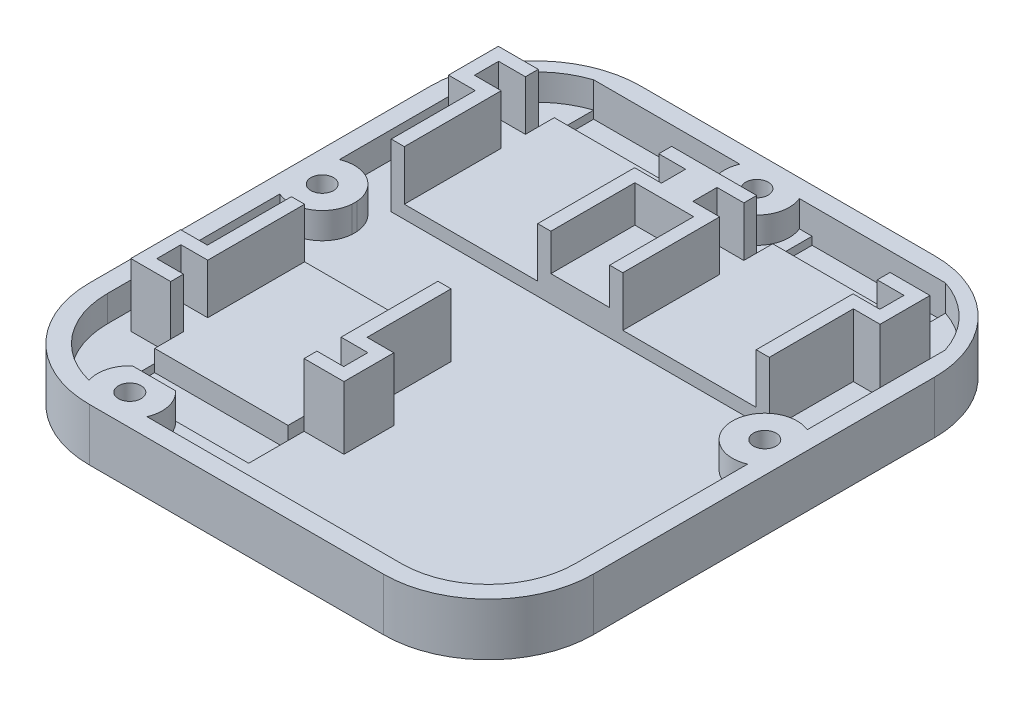
SolidWorks part; units mm, degrees
material "ABS"
ref_plane "Front Plane" through (0, 0, 0) normal (0, 0, 1) x (1, 0, 0)
ref_plane "Top Plane" through (0, 0, 0) normal (0, 1, 0) x (1, 0, 0)
ref_plane "Right Plane" through (0, 0, 0) normal (1, 0, 0) x (0, 0, -1)
sketch "Sketch1" plane through (0, 0, 0) normal (0, 1, 0) x (1, 0, 0)
  line L0 (-28, 52.5) -> (28, 52.5)
  line L1 (48, 32.5) -> (48, -32.5)
  line L2 (28, -52.5) -> (-28, -52.5)
  line L3 (-48, -32.5) -> (-48, 32.5)
  line L4 (0, 52.5) -> (0, -52.5) construction
  line L5 (-48, 0) -> (48, 0) construction
  arc A0 (-28, -52.5) -> (-48, -32.5) centre (-28, -32.5) cw
  arc A1 (48, -32.5) -> (28, -52.5) centre (28, -32.5) cw
  arc A2 (48, 32.5) -> (28, 52.5) centre (28, 32.5) ccw
  arc A3 (-28, 52.5) -> (-48, 32.5) centre (-28, 32.5) ccw
  point P8 (0, 0)
  point P14 (48, -52.5)
  point P17 (48, 52.5)
  point P20 (-48, 52.5)
  dimension "D1" = 96
  dimension "D3" = 20
  dimension "D2" = 105
extrude "base" add sketch "Sketch1" along normal blind 10
sketch "Sketch10" plane through (0, 10, 0) normal (0, 1, 0) x (1, 0, 0)
  line L0 (-41.1, -22) -> (-41.1, -31.5) construction
  line L1 (-41.1, -31.5) -> (-0.5, -31.5) construction
  line L2 (-41.1, -22) -> (-41.1, -31.5)
  line L3 (-41.1, -31.5) -> (-0.5, -31.5)
  line L4 (-28, -52.5) -> (28, -52.5)
  line L5 (-48, 32.5) -> (-48, -32.5)
  line L6 (28, 52.5) -> (-28, 52.5)
  line L7 (48, -32.5) -> (48, 32.5)
  line L8 (-28, -52.5) -> (28, -52.5)
  line L9 (-48, 32.5) -> (-48, -32.5)
  line L10 (28, 52.5) -> (-28, 52.5)
  line L11 (48, -32.5) -> (48, 32.5)
  line L12 (-3, -24.45) -> (-3, -29.05) construction
  line L13 (-3, -29.05) -> (-38.6, -29.05) construction
  line L14 (-38.6, -29.05) -> (-38.6, -24.45) construction
  line L15 (-38.6, -24.45) -> (-3, -24.45) construction
  line L16 (-41.1, -22) -> (-41.1, -31.5)
  line L17 (-41.1, -31.5) -> (-0.5, -31.5)
  line L18 (-0.5, -31.5) -> (-0.5, -22)
  line L19 (-0.5, -22) -> (-8.6, -22)
  line L20 (-8.6, -22) -> (-8.6, -6)
  line L21 (-8.6, -6) -> (-33, -6)
  line L22 (-33, -6) -> (-33, -22)
  line L23 (-33, -22) -> (-41.1, -22)
  line L24 (-41.1, -22) -> (-41.1, -31.5)
  line L25 (-41.1, -31.5) -> (-0.5, -31.5)
  line L26 (-0.5, -31.5) -> (-0.5, -22)
  line L27 (-0.5, -22) -> (-8.6, -22)
  line L28 (-8.6, -22) -> (-8.6, -6)
  line L29 (-8.6, -6) -> (-33, -6)
  line L30 (-33, -6) -> (-33, -22)
  line L31 (-33, -22) -> (-41.1, -22)
  line L32 (-12.6, -10) -> (-12.6, -22) construction
  line L33 (-12.6, -22) -> (-29, -22) construction
  line L34 (-29, -22) -> (-29, -10) construction
  line L35 (-29, -10) -> (-12.6, -10) construction
  line L36 (41.1, 29) -> (41.1, 38.5)
  line L37 (41.1, 38.5) -> (-41.1, 38.5)
  line L38 (-41.1, 38.5) -> (-41.1, 29)
  line L39 (-41.1, 29) -> (-33, 29)
  line L40 (-33, 29) -> (-33, 13)
  line L41 (-33, 13) -> (-8.6, 13)
  line L42 (-8.6, 13) -> (-8.6, 29)
  line L43 (-8.6, 29) -> (8.6, 29)
  line L44 (8.6, 29) -> (8.6, 13)
  line L45 (8.6, 13) -> (33, 13)
  line L46 (33, 13) -> (33, 29)
  line L47 (33, 29) -> (41.1, 29)
  line L48 (41.1, 29) -> (41.1, 38.5)
  line L49 (41.1, 38.5) -> (-41.1, 38.5)
  line L50 (-41.1, 38.5) -> (-41.1, 29)
  line L51 (-41.1, 29) -> (-33, 29)
  line L52 (-33, 29) -> (-33, 13)
  line L53 (-33, 13) -> (-8.6, 13)
  line L54 (-8.6, 13) -> (-8.6, 29)
  line L55 (-8.6, 29) -> (8.6, 29)
  line L56 (8.6, 29) -> (8.6, 13)
  line L57 (8.6, 13) -> (33, 13)
  line L58 (33, 13) -> (33, 29)
  line L59 (33, 29) -> (41.1, 29)
  line L60 (-29, 17) -> (-29, 29) construction
  line L61 (-29, 29) -> (-12.6, 29) construction
  line L62 (-12.6, 29) -> (-12.6, 17) construction
  line L63 (-12.6, 17) -> (-29, 17) construction
  line L64 (-3, 36.05) -> (-3, 31.45) construction
  line L65 (-3, 31.45) -> (-38.6, 31.45) construction
  line L66 (-38.6, 31.45) -> (-38.6, 36.05) construction
  line L67 (-38.6, 36.05) -> (-3, 36.05) construction
  line L68 (29, 29) -> (29, 17) construction
  line L69 (29, 17) -> (12.6, 17) construction
  line L70 (12.6, 17) -> (12.6, 29) construction
  line L71 (12.6, 29) -> (29, 29) construction
  line L72 (3, 31.45) -> (3, 36.05) construction
  line L73 (3, 36.05) -> (38.6, 36.05) construction
  line L74 (38.6, 36.05) -> (38.6, 31.45) construction
  line L75 (38.6, 31.45) -> (3, 31.45) construction
  line L76 (-3, -24.45) -> (-3, -29.05)
  line L77 (-3, -29.05) -> (-38.6, -29.05)
  line L78 (-38.6, -29.05) -> (-38.6, -24.45)
  line L79 (-38.6, -24.45) -> (-3, -24.45)
  line L80 (-12.6, -10) -> (-12.6, -22)
  line L81 (-12.6, -22) -> (-29, -22)
  line L82 (-29, -22) -> (-29, -10)
  line L83 (-29, -10) -> (-12.6, -10)
  line L84 (-29, 17) -> (-29, 29)
  line L85 (-29, 29) -> (-12.6, 29)
  line L86 (-12.6, 29) -> (-12.6, 17)
  line L87 (-12.6, 17) -> (-29, 17)
  line L88 (-3, 36.05) -> (-3, 31.45)
  line L89 (-3, 31.45) -> (-38.6, 31.45)
  line L90 (-38.6, 31.45) -> (-38.6, 36.05)
  line L91 (-38.6, 36.05) -> (-3, 36.05)
  line L92 (29, 29) -> (29, 17)
  line L93 (29, 17) -> (12.6, 17)
  line L94 (12.6, 17) -> (12.6, 29)
  line L95 (12.6, 29) -> (29, 29)
  line L96 (3, 31.45) -> (3, 36.05)
  line L97 (3, 36.05) -> (38.6, 36.05)
  line L98 (38.6, 36.05) -> (38.6, 31.45)
  line L99 (38.6, 31.45) -> (3, 31.45)
  line L100 (-33, 13) -> (-36, 13)
  line L101 (-36, 13) -> (-36, 5.5)
  line L102 (-36, 5.5) -> (-5.6, 5.5)
  line L103 (-5.6, 5.5) -> (-5.6, 13)
  line L104 (-5.6, 13) -> (-8.6, 13)
  line L105 (0, 0) -> (0, 38.5) construction
  line L106 (0, 0) -> (-48, 0) construction
  line L107 (5.6, 13) -> (8.6, 13)
  line L108 (5.6, 5.5) -> (5.6, 13)
  line L109 (36, 5.5) -> (5.6, 5.5)
  line L110 (36, 13) -> (36, 5.5)
  line L111 (33, 13) -> (36, 13)
  line L112 (33, 13) -> (8.6, 13)
  line L113 (-33, -6) -> (-36, -6)
  line L114 (-36, -6) -> (-36, 1.5)
  line L115 (-36, 1.5) -> (-5.6, 1.5)
  line L116 (-5.6, 1.5) -> (-5.6, -6)
  line L117 (-5.6, -6) -> (-8.6, -6)
  line L118 (-20.8, -31.5) -> (-20.8, 1.5) construction
  line L119 (-20.8, 5.5) -> (-20.8, 38.5) construction
  arc A4 (28, -52.5) -> (48, -32.5) centre (28, -32.5) ccw
  arc A5 (-48, -32.5) -> (-28, -52.5) centre (-28, -32.5) ccw
  arc A6 (-28, 52.5) -> (-48, 32.5) centre (-28, 32.5) ccw
  arc A7 (48, 32.5) -> (28, 52.5) centre (28, 32.5) ccw
  arc A8 (28, -52.5) -> (48, -32.5) centre (28, -32.5) ccw
  arc A9 (-48, -32.5) -> (-28, -52.5) centre (-28, -32.5) ccw
  arc A10 (-28, 52.5) -> (-48, 32.5) centre (-28, 32.5) ccw
  arc A11 (48, 32.5) -> (28, 52.5) centre (28, 32.5) ccw
  dimension "D4" = 7.5
  dimension "D5" = 7.5
  dimension "D6" = 30.4
  dimension "D1" = 0
  dimension "D2" = 0
  dimension "D3" = 0
extrude "hole for actuator covers" cut sketch "Sketch10" against normal blind 5 contours L103 L104 L53 L100 L101 L102 | L111 L57 L107 L108 L109 L110 | L117 L116 L115 L114 L113 L29
sketch "Sketch13" plane through (0, 10, 0) normal (0, 1, 0) x (1, 0, 0)
  line L0 (-41.1, 29) -> (-33, 29) construction
  line L1 (-33, 29) -> (-33, 13) construction
  line L2 (-8.6, 13) -> (-8.6, 29) construction
  line L3 (-8.6, 29) -> (8.6, 29) construction
  line L4 (8.6, 29) -> (8.6, 13) construction
  line L5 (33, 13) -> (33, 29) construction
  line L6 (33, 29) -> (41.1, 29) construction
  line L7 (-41.1, 29) -> (-33, 29) construction
  line L8 (-33, 29) -> (-33, 13) construction
  line L9 (-8.1, -24.45) -> (-3, -24.45)
  line L10 (-8.6, 13) -> (-8.6, 29) construction
  line L11 (-8.6, 29) -> (8.6, 29) construction
  line L12 (-8.1, -21.5) -> (-8.1, -6) construction
  line L13 (8.6, 29) -> (8.6, 13) construction
  line L14 (33, 13) -> (33, 29) construction
  line L15 (-41.1, 29) -> (-41.1, 38.5)
  line L16 (33, 29) -> (41.1, 29) construction
  line L17 (-33.5, 31.45) -> (-38.6, 31.45)
  line L18 (-33.5, 31.45) -> (-33.5, 13)
  line L19 (-8.1, 13) -> (-8.1, 31.45)
  line L20 (-3, 31.45) -> (-38.6, 31.45) construction
  line L21 (-41.1, 38.5) -> (-33.5, 38.5)
  line L22 (8.1, 31.45) -> (8.1, 13)
  line L23 (33.5, 13) -> (33.5, 31.45)
  line L25 (-3, 31.45) -> (-3, 36.05)
  line L26 (-41.1, 29) -> (-36, 29)
  line L27 (-36, 29) -> (-36, 13)
  line L28 (-33, 13) -> (-36, 13) construction
  line L29 (-36, 13) -> (-33.5, 13)
  line L30 (-8.1, 13) -> (-5.6, 13)
  line L31 (-5.6, 13) -> (-8.6, 13) construction
  line L32 (-5.6, 13) -> (-5.6, 29)
  line L33 (-5.6, 29) -> (5.6, 29)
  line L34 (5.6, 29) -> (5.6, 13)
  line L35 (5.6, 13) -> (8.6, 13) construction
  line L36 (5.6, 13) -> (8.1, 13)
  line L37 (33.5, 13) -> (36, 13)
  line L38 (33, 13) -> (36, 13) construction
  line L39 (36, 13) -> (36, 29)
  line L40 (36, 29) -> (41.1, 29)
  line L41 (-38.6, -24.45) -> (-38.6, -29.05)
  line L42 (-33, -6) -> (-33, -22) construction
  line L43 (-33, -22) -> (-41.1, -22) construction
  line L44 (-0.5, -22) -> (-8.6, -22) construction
  line L45 (-8.6, -22) -> (-8.6, -6) construction
  line L46 (-33, -6) -> (-33, -22) construction
  line L47 (-33, -22) -> (-41.1, -22) construction
  line L48 (-0.5, -22) -> (-8.6, -22) construction
  line L49 (-8.6, -22) -> (-8.6, -6) construction
  line L50 (-33.5, -6) -> (-33.5, -24.45)
  line L51 (-33.5, -24.45) -> (-38.6, -24.45)
  line L52 (-38.6, -24.45) -> (-3, -24.45) construction
  line L53 (-8.1, -24.45) -> (-8.1, -6)
  line L54 (-33.5, -6) -> (-36, -6)
  line L55 (-33, -6) -> (-36, -6) construction
  line L56 (-36, -6) -> (-36, -22)
  line L57 (-36, -22) -> (-41.1, -22)
  line L58 (-0.5, -22) -> (-0.5, -31.5)
  line L59 (-8.1, -6) -> (-5.6, -6)
  line L60 (-5.6, -6) -> (-8.6, -6) construction
  line L61 (-5.6, -6) -> (-5.6, -22)
  line L62 (-5.6, -22) -> (-0.5, -22)
  line L66 (-41.1, 28.5) -> (-33.5, 28.5) construction
  line L67 (-8.1, 28.5) -> (8.1, 28.5) construction
  line L68 (33.5, 28.5) -> (41.1, 28.5) construction
  line L69 (-33.5, 28.5) -> (-33.5, 13) construction
  line L70 (-8.1, 31.45) -> (-3, 31.45)
  line L71 (38.6, 31.45) -> (3, 31.45) construction
  line L72 (8.1, 28.5) -> (8.1, 13) construction
  line L73 (-8.1, 13) -> (-8.1, 28.5) construction
  line L74 (33.5, 31.45) -> (38.6, 31.45)
  line L76 (33.5, 13) -> (33.5, 28.5) construction
  line L77 (-33.5, -21.5) -> (-41.1, -21.5) construction
  line L78 (-0.5, -21.5) -> (-8.1, -21.5) construction
  line L79 (-33.5, -6) -> (-33.5, -21.5) construction
  line L80 (41.1, 38.5) -> (-41.1, 38.5) construction
  line L81 (-33.5, 38.5) -> (-33.5, 36.05)
  line L82 (-38.6, 36.05) -> (-3, 36.05) construction
  line L83 (-33.5, 36.05) -> (-38.6, 36.05)
  line L84 (-38.6, 36.05) -> (-38.6, 31.45)
  line L85 (-3, 36.05) -> (-8.1, 36.05)
  line L86 (-8.1, 36.05) -> (-8.1, 38.5)
  line L87 (-8.1, 38.5) -> (8.1, 38.5)
  line L88 (8.1, 38.5) -> (8.1, 36.05)
  line L89 (3, 36.05) -> (38.6, 36.05) construction
  line L90 (8.1, 36.05) -> (3, 36.05)
  line L91 (3, 36.05) -> (3, 31.45)
  line L92 (3, 31.45) -> (8.1, 31.45)
  line L93 (38.6, 31.45) -> (38.6, 36.05)
  line L94 (38.6, 36.05) -> (33.5, 36.05)
  line L95 (33.5, 36.05) -> (33.5, 38.5)
  line L96 (33.5, 38.5) -> (41.1, 38.5)
  line L97 (41.1, 38.5) -> (41.1, 29)
  line L98 (-38.6, -29.05) -> (-33.5, -29.05)
  line L99 (-3, -29.05) -> (-38.6, -29.05) construction
  line L100 (-33.5, -29.05) -> (-33.5, -31.5)
  line L101 (-41.1, -31.5) -> (-0.5, -31.5) construction
  line L102 (-33.5, -31.5) -> (-41.1, -31.5)
  line L103 (-41.1, -31.5) -> (-41.1, -22)
  line L104 (-0.5, -31.5) -> (-8.1, -31.5)
  line L105 (-8.1, -31.5) -> (-8.1, -29.05)
  line L106 (-8.1, -29.05) -> (-3, -29.05)
  line L107 (-3, -29.05) -> (-3, -24.45)
  dimension "D1" = 0.5
  dimension "D3" = 2.5
  dimension "D5" = 2.5
  dimension "D6" = 2.5
  dimension "D8" = 2.5
  dimension "D10" = 2.5
  dimension "D12" = 2.5
  dimension "D9" = 0.5
extrude "side clamps" add sketch "Sketch13" along normal blind 7
sketch "Sketch14" plane through (0, 10, 0) normal (0, 1, 0) x (1, 0, 0)
  line L0 (-33.5, -34.55) -> (-8.1, -34.55)
  line L1 (-8.1, -34.55) -> (-8.1, -42.05)
  line L2 (-8.1, -42.05) -> (-33.5, -42.05)
  line L3 (-33.5, -42.05) -> (-33.5, -34.55)
  line L7 (-33.5, 41.55) -> (-8.1, 41.55)
  line L8 (-8.1, 41.55) -> (-8.1, 49.05)
  line L9 (-8.1, 49.05) -> (-33.5, 49.05)
  line L10 (-33.5, 49.05) -> (-33.5, 41.55)
  line L13 (0, 0) -> (0, 52.5) construction
  line L14 (28, 52.5) -> (-28, 52.5) construction
  line L15 (33.5, 49.05) -> (33.5, 41.55)
  line L16 (8.1, 49.05) -> (33.5, 49.05)
  line L17 (8.1, 41.55) -> (8.1, 49.05)
  line L18 (33.5, 41.55) -> (8.1, 41.55)
  line L19 (-3, -29.05) -> (-38.6, -29.05) construction
  line L20 (-38.6, 36.05) -> (-3, 36.05) construction
  line L21 (-33.5, 13) -> (-33.5, 31.45) construction
  line L22 (-8.1, 31.45) -> (-8.1, 13) construction
  line L23 (-33.5, -24.45) -> (-33.5, -6) construction
  line L24 (-8.1, -6) -> (-8.1, -24.45) construction
  dimension "D1" = 5.5
  dimension "D2" = 7.5
  dimension "D3" = 5.5
  dimension "D4" = 7.5
extrude "pulley clearances" cut sketch "Sketch14" against normal blind 6.5
sketch "Sketch15" plane through (0, 10, 0) normal (0, 1, 0) x (1, 0, 0)
  line L0 (-42.1421, -46.6421) -> (-42.1421, 46.6421) construction
  line L1 (48, 6) -> (-48, 6) construction
  line L2 (48, -32.5) -> (48, 32.5) construction
  line L3 (-48, 32.5) -> (-48, -32.5) construction
  line L4 (-36, 1.5) -> (-5.6, 1.5) construction
  line L5 (-42.1421, -46.6421) -> (42.1421, -46.6421) construction
  line L6 (-42.1421, 46.6421) -> (42.1421, 46.6421) construction
  line L7 (42.1421, 46.6421) -> (42.1421, -46.6421) construction
  line L8 (0, 52.5) -> (0, -52.5) construction
  line L9 (28, 52.5) -> (-28, 52.5) construction
  line L10 (-28, -52.5) -> (28, -52.5) construction
  line L11 (-26.1421, -52.5) -> (-26.1421, 52.5) construction
  arc A0 (-48, -32.5) -> (-28, -52.5) centre (-28, -32.5) ccw construction
  arc A1 (-28, 52.5) -> (-48, 32.5) centre (-28, 32.5) ccw construction
  circle A2 centre (-42.1421, 6) radius 3.175
  circle A3 centre (42.1421, 6) radius 3.175
  circle A4 centre (-26.1421, -46.6421) radius 3.175
  arc A5 (28, -52.5) -> (48, -32.5) centre (28, -32.5) ccw construction
  circle A6 centre (0, 46.6421) radius 3.175
  arc A7 (48, 32.5) -> (28, 52.5) centre (28, 32.5) ccw construction
  dimension "D1" = 6.35
  dimension "D3" = 16
  dimension "D2" = 4.5
hole_wizard "CSK for #8 Flat Head Socket Cap Screw1" positions "Sketch17" profile "Sketch16" countersink size "#8" standard "ANSI Inch"
sketch "Sketch17" plane through (0, 0, 0) normal (0, -1, 0) x (-1, 0, 0)
  point P0 (26.1421, -46.6421)
  point P3 (42.1421, 6)
  point P6 (0, 46.6421)
  point P9 (-42.1421, 6)
sketch "Sketch16" plane through (-26.1421, 0, 46.6421) normal (1, 0, 0) x (0, 0, -1)
  line L0 (0, 0) -> (0, 11.2924)
  line L1 (0, 11.2924) -> (2.1526, 9.999)
  line L2 (2.1526, 9.999) -> (2.1526, 2.7685)
  line L3 (2.1526, 2.7685) -> (4.5593, 0)
  line L5 (4.5593, 0) -> (0, 0)
  line L6 (-2.1527, 2.7685) -> (-4.5593, 0) construction
  line L10 (0, 11.2924) -> (-2.1527, 9.999) construction
  line L11 (0, -6.35) -> (0, 107.95) construction
  dimension "Hole Dia." = 4.3053
  dimension "Hole Depth" = 9.999
  dimension "Near C'Sink Dia." = 9.1186
  dimension "Near C'Sink Angle" = 82
  dimension "Drill Angle" = 118
sketch "Sketch18" plane through (0, 10, 0) normal (0, 1, 0) x (1, 0, 0)
  line L0 (-33.5, 13) -> (-8.1, 13)
  line L1 (-20.8, 5.5) -> (-20.8, 41.55) construction
  line L2 (-36, 5.5) -> (-5.6, 5.5) construction
  line L3 (-33.5, 41.55) -> (-8.1, 41.55) construction
  line L4 (-33.5, 41.55) -> (-8.1, 41.55)
  line L5 (-3, 36.05) -> (-8.1, 36.05)
  line L6 (-3, 31.45) -> (-3, 36.05)
  line L7 (-8.1, 31.45) -> (-3, 31.45)
  line L8 (-8.1, 13) -> (-8.1, 31.45)
  line L9 (-8.1, 36.05) -> (-8.1, 41.55)
  line L10 (-33.5, 36.05) -> (-33.5, 38.5)
  line L11 (-33.5, 38.5) -> (-41.1, 38.5)
  line L12 (-41.1, 38.5) -> (-41.1, 29)
  line L13 (-41.1, 29) -> (-36, 29)
  line L14 (-36, 29) -> (-36, 13)
  line L15 (-36, 13) -> (-33.5, 13)
  line L16 (-33.5, 13) -> (-33.5, 31.45)
  line L17 (-33.5, 31.45) -> (-38.6, 31.45)
  line L18 (-38.6, 31.45) -> (-38.6, 36.05)
  line L19 (-38.6, 36.05) -> (-33.5, 36.05)
  line L20 (-33.5, 36.05) -> (-33.5, 41.55)
  line L21 (0, 0) -> (0, 52.5) construction
  line L22 (28, 52.5) -> (-28, 52.5) construction
  line L23 (20.8, 5.5) -> (20.8, 41.55) construction
  line L24 (38.6, 36.05) -> (33.5, 36.05)
  line L25 (38.6, 31.45) -> (38.6, 36.05)
  line L26 (-33.5, 13) -> (-33.5, 31.45)
  line L27 (-33.5, 31.45) -> (-38.6, 31.45)
  line L28 (-38.6, 31.45) -> (-38.6, 36.05)
  line L29 (-38.6, 36.05) -> (-33.5, 36.05)
  line L30 (33.5, 31.45) -> (38.6, 31.45)
  line L31 (33.5, 13) -> (33.5, 31.45)
  line L32 (33.5, 36.05) -> (33.5, 41.55)
  line L33 (8.1, 36.05) -> (8.1, 41.55)
  line L34 (8.1, 13) -> (8.1, 31.45)
  line L35 (8.1, 31.45) -> (3, 31.45)
  line L36 (3, 31.45) -> (3, 36.05)
  line L37 (3, 36.05) -> (8.1, 36.05)
  line L38 (33.5, 41.55) -> (8.1, 41.55)
  line L39 (33.5, 13) -> (8.1, 13)
  line L40 (-33.5, -24.45) -> (-33.5, -6) construction
  line L41 (-33.5, -24.45) -> (-33.5, -6)
  line L42 (-38.6, -24.45) -> (-33.5, -24.45) construction
  line L43 (-38.6, -29.05) -> (-38.6, -24.45) construction
  line L44 (-33.5, -29.05) -> (-38.6, -29.05) construction
  line L45 (-33.5, -31.5) -> (-33.5, -29.05) construction
  line L46 (-38.6, -24.45) -> (-33.5, -24.45)
  line L47 (-38.6, -29.05) -> (-38.6, -24.45)
  line L48 (-33.5, -29.05) -> (-38.6, -29.05)
  line L49 (-33.5, -34.55) -> (-33.5, -29.05)
  line L50 (-20.8, 1.5) -> (-20.8, -42.05) construction
  line L51 (-36, 1.5) -> (-5.6, 1.5) construction
  line L52 (-33.5, -42.05) -> (-8.1, -42.05) construction
  line L53 (-33.5, -34.55) -> (-8.1, -34.55)
  line L54 (-33.5, -6) -> (-8.1, -6)
  line L55 (-8.1, -34.55) -> (-8.1, -29.05)
  line L56 (-8.1, -29.05) -> (-3, -29.05)
  line L57 (-3, -29.05) -> (-3, -24.45)
  line L58 (-3, -24.45) -> (-8.1, -24.45)
  line L59 (-8.1, -24.45) -> (-8.1, -6)
  line L60 (-33.5, -31.5) -> (-33.5, -29.05)
  point P20 (-20.8, 13)
  point P42 (20.8, 13)
  point P62 (-20.8, -6)
  dimension "D1" = 0
extrude "actuator groove" cut sketch "Sketch18" against normal blind 2.5
sketch "Sketch20" plane through (0, 10, 0) normal (0, 1, 0) x (1, 0, 0)
  line L0 (-36, -6) -> (-5.6, -6)
  line L1 (-8.1, 49.05) -> (-5.6726, 49.05)
  line L2 (-5.6, -6) -> (-5.6, -22)
  line L3 (-8.1, 38.5) -> (-8.1, 49.05) construction
  line L4 (-0.5, -31.5) -> (-8.1, -31.5)
  line L5 (-8.1, 38.5) -> (-8.1, 41.55)
  line L6 (33.5, 38.5) -> (33.5, 41.55)
  line L7 (-8.1, 38.5) -> (8.1, 38.5)
  line L8 (8.1, 38.5) -> (8.1, 41.55)
  line L9 (8.1, 49.05) -> (8.1, 41.55) construction
  line L10 (8.1, 49.05) -> (5.6726, 49.05)
  line L11 (-8.1, -31.5) -> (-8.1, -42.05)
  line L12 (-20.4696, -49.05) -> (28, -49.05)
  line L13 (-28, -49.05) -> (28, -49.05)
  line L14 (44.55, -32.5) -> (44.55, 32.5)
  line L15 (44.55, -32.5) -> (44.55, 0.3274)
  line L16 (33.5, 49.05) -> (8.1, 49.05) construction
  line L17 (-41.1, 29) -> (-36, 29)
  line L18 (-8.1, 49.05) -> (-33.5, 49.05) construction
  line L19 (-33.5, -42.05) -> (-30.2517, -42.05)
  line L20 (-22.0326, -42.05) -> (-8.1, -42.05)
  line L21 (-36, 13) -> (36, 13)
  line L22 (44.55, 11.6726) -> (44.55, 37.9485)
  line L23 (41.1, 29) -> (36, 29)
  line L24 (36, 29) -> (36, 13)
  line L25 (-8.1, 41.55) -> (-33.5, 41.55)
  line L26 (8.1, 41.55) -> (33.5, 41.55)
  line L27 (-44.55, 11.6726) -> (-44.55, 37.9485)
  line L29 (-36, 29) -> (-36, 13)
  line L30 (-41.1, 29) -> (-36, 29) construction
  line L31 (-44.55, 0.3274) -> (-44.55, -32.5)
  line L32 (-36, -6) -> (-36, -22)
  line L33 (-36, -22) -> (-41.1, -22)
  line L34 (36, 29) -> (41.1, 29) construction
  line L35 (8.1, 49.05) -> (33.5, 49.05)
  line L36 (-5.6, -22) -> (-0.5, -22)
  line L37 (-0.5, -22) -> (-0.5, -31.5)
  line L38 (-8.1, 49.05) -> (-33.5, 49.05)
  line L39 (-8.1, -42.05) -> (-8.1, -31.5) construction
  line L42 (-41.1, -22) -> (-41.1, -31.5)
  line L43 (-41.1, -31.5) -> (-33.5, -31.5)
  line L45 (-33.5, -31.5) -> (-33.5, -42.05)
  line L49 (-8.1, -31.5) -> (-0.5, -31.5) construction
  line L50 (-41.1, 29) -> (-41.1, 38.5)
  line L51 (-41.1, 38.5) -> (-33.5, 38.5)
  line L53 (-33.5, 38.5) -> (-33.5, 41.55)
  line L54 (41.1, 29) -> (41.1, 38.5)
  line L55 (41.1, 38.5) -> (33.5, 38.5)
  arc A0 (36, 5.5) -> (44.55, 0.3274) centre (42.1421, 6) ccw
  arc A1 (-5.6726, 49.05) -> (5.6726, 49.05) centre (0, 46.6421) ccw
  arc A2 (-28, 52.5) -> (-48, 32.5) centre (-28, 32.5) ccw construction
  arc A3 (-20.4696, -49.05) -> (-22.0326, -42.05) centre (-26.1421, -46.6421) ccw
  arc A4 (36, 5.5) -> (44.55, 11.6726) centre (42.1421, 6) cw
  arc A5 (28, -49.05) -> (44.55, -32.5) centre (28, -32.5) ccw
  arc A6 (28, -49.05) -> (44.55, -32.5) centre (28, -32.5) ccw
  arc A7 (-44.55, 0.3274) -> (-44.55, 11.6726) centre (-42.1421, 6) ccw
  arc A8 (-30.2517, -42.05) -> (-31.9987, -48.5597) centre (-26.1421, -46.6421) ccw
  arc A9 (48, 32.5) -> (28, 52.5) centre (28, 32.5) ccw construction
  arc A11 (-44.55, -32.5) -> (-28, -49.05) centre (-28, -32.5) ccw
  arc A12 (-44.55, -32.5) -> (-31.9987, -48.5597) centre (-28, -32.5) ccw
  arc A14 (44.55, 37.9485) -> (33.5, 49.05) centre (28.0126, 32.5379) ccw
  arc A20 (-33.5, 49.05) -> (-44.55, 37.9485) centre (-28.0126, 32.5379) ccw
  dimension "D3" = 3.45
  dimension "D1" = 3.45
  dimension "D5" = 17.4
  dimension "D6" = 0.04
  dimension "D2" = 17.4
  dimension "D4" = 0.04
extrude "material cutaway" cut sketch "Sketch20" against normal up to surface (5 mm away) up to face at (20.8, 5, -9.25)
